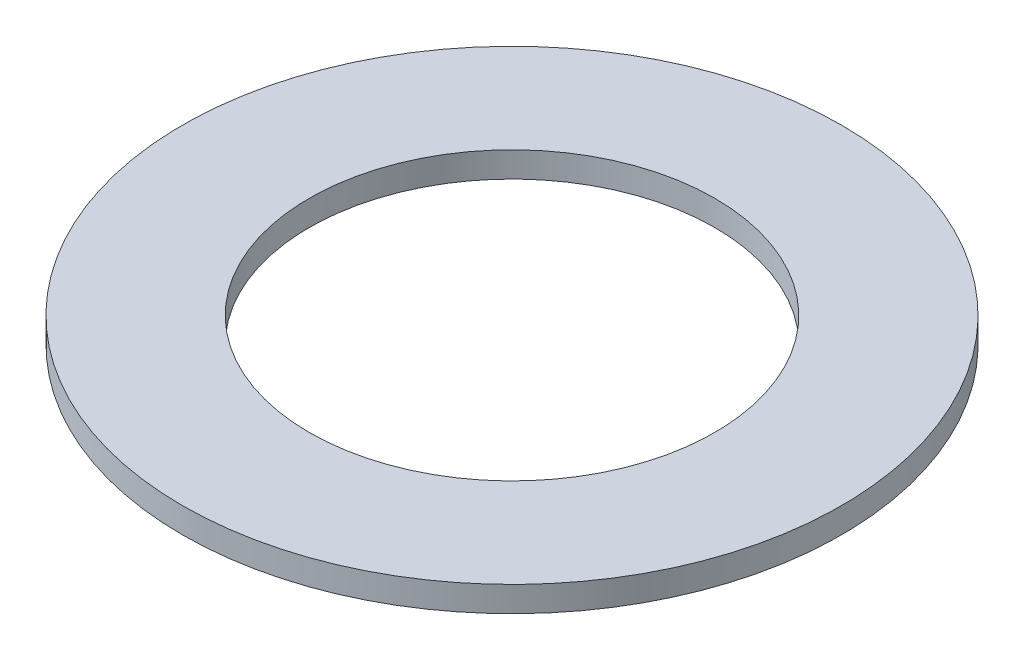
SolidWorks part; units mm, degrees
material "PTFE (general)"
ref_plane "Front Plane" through (0, 0, 0) normal (0, 0, 1) x (1, 0, 0)
ref_plane "Top Plane" through (0, 0, 0) normal (0, 1, 0) x (1, 0, 0)
ref_plane "Right Plane" through (0, 0, 0) normal (1, 0, 0) x (0, 0, -1)
sketch "Sketch1" plane through (0, 0, 0) normal (0, 1, 0) x (1, 0, 0)
  circle A0 centre (0, 0) radius 4
  circle A1 centre (0, 0) radius 6.5
extrude "Boss-Extrude1" add sketch "Sketch1" along normal blind 0.5
